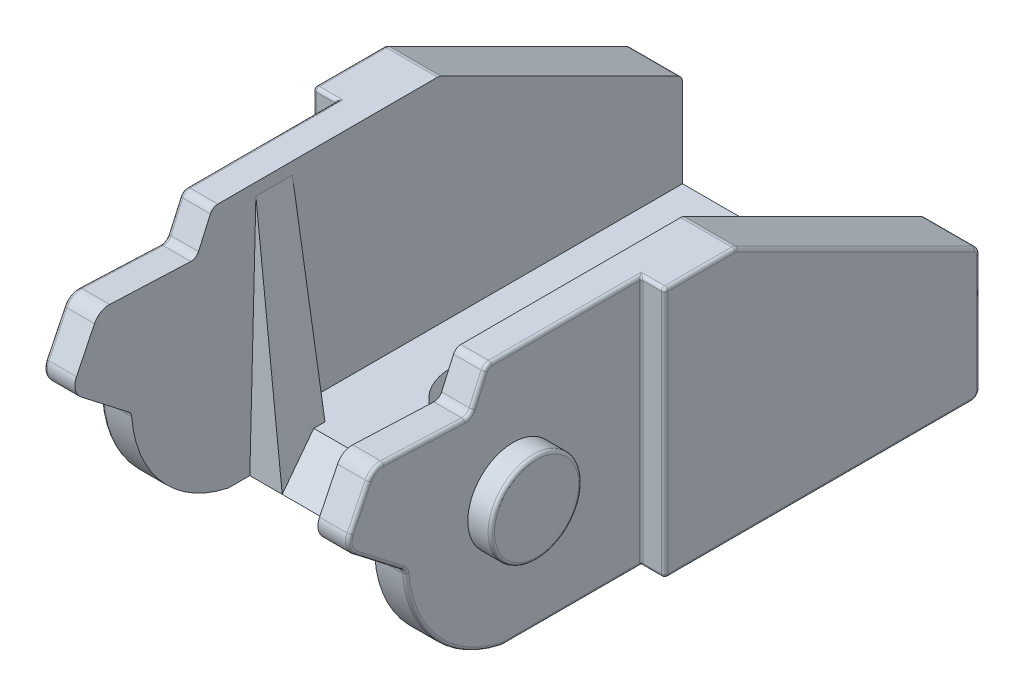
SolidWorks part; units mm, degrees
material "ABS"
ref_plane "Front Plane" through (0, 0, 0) normal (0, 0, 1) x (1, 0, 0)
ref_plane "Top Plane" through (0, 0, 0) normal (0, 1, 0) x (1, 0, 0)
ref_plane "Right Plane" through (0, 0, 0) normal (1, 0, 0) x (0, 0, -1)
sketch "Sketch1" plane through (0, 0, 0) normal (1, 0, 0) x (0, 0, -1)
  line L0 (0, 0) -> (-2.8, 0) construction
  line L1 (0, 0) -> (2.8, 0) construction
  line L2 (2.8, 0) -> (7.9, 0) construction
  line L3 (7.9, 0) -> (27.35, 0) construction
  line L4 (0, 0) -> (0, 2.8) construction
  line L5 (0, 2.8) -> (0, 7.75) construction
  line L6 (0, 0) -> (0, -2.8) construction
  line L7 (0, -2.8) -> (0, -7.75) construction
  line L8 (-10.65, 7.75) -> (27.35, 7.75)
  line L9 (-10.65, -7.75) -> (27.35, -7.75)
  line L10 (27.35, 7.75) -> (27.35, -7.75)
  line L11 (-10.65, -7.75) -> (-10.65, 7.75)
  line L12 (7.9, 7.75) -> (7.9, -7.75) construction
  circle A0 centre (0, 0) radius 2.8 construction
  dimension "D1" = 5.6
  dimension "D2" = 27.35
  dimension "D3" = 5.1
  dimension "D4" = 15.5
  dimension "D5" = 38
extrude "Boss-Extrude1" add sketch "Sketch1" along normal mid plane 21.7
sketch "Sketch2" plane through (0, 0, 0) normal (1, 0, 0) x (0, 0, -1)
  line L0 (-10.65, 7.75) -> (-10.65, -7.75)
  line L1 (-10.65, -7.75) -> (-0.65, -7.75)
  line L3 (-10.65, -7.75) -> (27.35, -7.75) construction
  line L4 (-0.65, -7.75) -> (-0.65, -0.75) construction
  line L5 (-0.65, -0.75) -> (-6.65, -0.75) construction
  line L6 (-6.65, -0.75) -> (-10.4, 2.1531)
  line L7 (-10.4, 2.1531) -> (-8.65, 5.75)
  line L8 (-8.65, 5.75) -> (-2.6552, 5.5)
  line L9 (-2.6552, 5.5) -> (-1.65, 7.75)
  line L10 (27.35, 7.75) -> (-10.65, 7.75) construction
  line L11 (-10.4, 2.1531) -> (-10.4, -0.75) construction
  line L12 (-10.4, -0.75) -> (-6.65, -0.75) construction
  line L13 (-1.65, 7.75) -> (-10.65, 7.75)
  arc A0 (-6.65, -0.75) -> (-0.65, -7.75) centre (0.8418, -0.3999) ccw
  dimension "D4" = 7.5
  dimension "D1" = 10
  dimension "D2" = 7
  dimension "D3" = 6
  dimension "D5" = 2.25
  dimension "D6" = 2
  dimension "D7" = 7
  dimension "D8" = 6
  dimension "D9" = 4
  dimension "D10" = 3.75
  dimension "D11" = 8.75
extrude "Cut-Extrude1" cut sketch "Sketch2" against normal through all both and the other way through all
fillet "Fillet1" radius 1 2 edges at (0, 5.75, 8.65) (0, 2.1531, 10.4)
fillet "Fillet2" radius 0.5 4 edges at (0, -7.75, 0.65) (0, -0.75, 6.65) (0, 5.5, 2.6552) (0, 7.75, 1.65)
sketch "Sketch4" plane through (10.85, 0, 0) normal (1, 0, 0) x (0, 0, -1)
  line L0 (7.9, 7.75) -> (7.9, -7.75) construction
  line L1 (7.9, 7.75) -> (7.9, -7.75)
  line L7 (-0.5989, -7.75) -> (27.35, -7.75)
  line L8 (27.35, -7.75) -> (27.35, 7.75)
  line L9 (27.35, 7.75) -> (-1.3258, 7.75)
  line L10 (-1.7823, 7.454) -> (-2.5168, 5.8097)
  line L11 (-2.9942, 5.5141) -> (-7.9956, 5.7227)
  line L12 (-8.9365, 5.1611) -> (-10.0445, 2.8839)
  line L13 (-9.7574, 1.6556) -> (-6.829, -0.6114)
  line L14 (-0.5989, -7.75) -> (7.9, -7.75)
  line L16 (7.9, 7.75) -> (-1.3258, 7.75)
  line L17 (-1.7823, 7.454) -> (-2.5168, 5.8097)
  line L18 (-2.9942, 5.5141) -> (-7.9956, 5.7227)
  line L19 (-8.9365, 5.1611) -> (-10.0445, 2.8839)
  line L20 (-9.7574, 1.6556) -> (-6.829, -0.6114)
  circle A0 centre (0, 0) radius 2.8 construction
  circle A1 centre (0, 0) radius 2.8
  arc A7 (-6.6366, -0.9688) -> (-0.7018, -7.7393) centre (0.8418, -0.3999) ccw
  arc A8 (-0.7018, -7.7393) -> (-0.5989, -7.75) centre (-0.5989, -7.25) ccw
  arc A9 (-1.3258, 7.75) -> (-1.7823, 7.454) centre (-1.3258, 7.25) ccw
  arc A10 (-2.9942, 5.5141) -> (-2.5168, 5.8097) centre (-2.9733, 6.0137) ccw
  arc A11 (-7.9956, 5.7227) -> (-8.9365, 5.1611) centre (-8.0373, 4.7236) ccw
  arc A12 (-10.0445, 2.8839) -> (-9.7574, 1.6556) centre (-9.1452, 2.4464) ccw
  arc A13 (-6.6366, -0.9688) -> (-6.829, -0.6114) centre (-7.1351, -1.0068) ccw
  arc A14 (-6.6366, -0.9688) -> (-0.7018, -7.7393) centre (0.8418, -0.3999) ccw
  arc A15 (-0.7018, -7.7393) -> (-0.5989, -7.75) centre (-0.5989, -7.25) ccw
  arc A16 (-1.3258, 7.75) -> (-1.7823, 7.454) centre (-1.3258, 7.25) ccw
  arc A17 (-2.9942, 5.5141) -> (-2.5168, 5.8097) centre (-2.9733, 6.0137) ccw
  arc A18 (-7.9956, 5.7227) -> (-8.9365, 5.1611) centre (-8.0373, 4.7236) ccw
  arc A19 (-10.0445, 2.8839) -> (-9.7574, 1.6556) centre (-9.1452, 2.4464) ccw
  arc A20 (-6.6366, -0.9688) -> (-6.829, -0.6114) centre (-7.1351, -1.0068) ccw
  dimension "D1" = 0
extrude "Cut-Extrude2" cut sketch "Sketch4" against normal blind 1.45
mirror "Mirror1" about plane through (0, 0, 0) normal (1, 0, 0) of "Cut-Extrude2"
sketch "Sketch5" plane through (0, 0, -27.35) normal (0, 0, -1) x (-1, 0, 0)
  line L0 (0, 0) -> (0, 7.75) construction
  line L1 (-10.85, 7.75) -> (10.85, 7.75) construction
  line L2 (0, 0) -> (0, -5.5) construction
  line L3 (-7.5, 7.75) -> (7.5, 7.75)
  line L4 (-7.5, 7.75) -> (-7.5, -5.5)
  line L5 (-7.5, -5.5) -> (7.5, -5.5)
  line L6 (7.5, 7.75) -> (7.5, -5.5)
  line L7 (0, -5.5) -> (0, -7.75) construction
  line L8 (-10.85, -7.75) -> (10.85, -7.75) construction
  dimension "D1" = 2.25
  dimension "D2" = 15
extrude "Cut-Extrude3" cut sketch "Sketch5" against normal through all
sketch "Sketch6" plane through (10.85, 0, 0) normal (1, 0, 0) x (0, 0, -1)
  line L0 (27.35, -7.75) -> (27.35, 0.25) construction
  line L1 (27.35, -7.75) -> (27.35, 7.75) construction
  line L2 (27.35, 0.25) -> (27.35, 7.75)
  line L3 (27.35, 7.75) -> (12.35, 7.75)
  line L4 (27.35, 7.75) -> (7.9, 7.75) construction
  line L5 (12.35, 7.75) -> (27.35, 0.25)
  dimension "D1" = 8
  dimension "D2" = 15
extrude "Cut-Extrude4" cut sketch "Sketch6" against normal up to surface (21.7 mm away) up to face at (-10.85, 0, -17.625)
sketch "Sketch8" plane through (0, -7.75, 0) normal (0, -1, 0) x (1, 0, 0)
  line L0 (0, -27.35) -> (0, -0.65) construction
  line L1 (-7.5, 4.6571) -> (7.5, 4.6571)
  line L2 (-7.5, 4.6571) -> (-7.5, -0.65)
  line L3 (-7.5, -0.65) -> (7.5, -0.65)
  line L4 (7.5, 4.6571) -> (7.5, -0.65)
  line L5 (10.85, -27.35) -> (-10.85, -27.35) construction
  line L6 (0, -0.65) -> (0, 0) construction
  line L7 (0, 0) -> (0, 4.6571) construction
  line L8 (7.5, 4.6571) -> (-7.5, 4.6571) construction
  line L9 (-7.5, -27.35) -> (-7.5, -12.35) construction
  dimension "D1" = 26.7
extrude "Cut-Extrude5" cut sketch "Sketch8" against normal through all
sketch "Sketch9" plane through (0, -7.75, 0) normal (0, -1, 0) x (1, 0, 0)
  line L0 (0, -21.35) -> (0, -27.35) construction
  line L2 (0, -17.35) -> (0, -21.35) construction
  line L3 (0, -12.35) -> (0, -17.35) construction
  line L4 (0, -12.35) -> (0, -8.35) construction
  line L5 (0, -8.35) -> (0, -0.65) construction
  line L6 (-7.5, -0.65) -> (7.5, -0.65) construction
  line L7 (0, -0.65) -> (0, 0) construction
  line L8 (-1.5, -19.35) -> (1.5, -19.35) construction
  line L9 (-1.5, -17.35) -> (1.5, -17.35)
  line L10 (-1.5, -21.35) -> (1.5, -21.35)
  line L11 (-1.5, -10.35) -> (1.5, -10.35) construction
  line L12 (-1.5, -8.35) -> (1.5, -8.35)
  line L13 (-1.5, -12.35) -> (1.5, -12.35)
  line L14 (1.5, -19.35) -> (3.5, -19.35) construction
  line L15 (-1.5, -19.35) -> (-3.5, -19.35) construction
  line L16 (1.5, -10.35) -> (3.5, -10.35) construction
  line L17 (-1.5, -10.35) -> (-3.5, -10.35) construction
  line L18 (10.85, -27.35) -> (-10.85, -27.35) construction
  arc A0 (-1.5, -17.35) -> (-1.5, -21.35) centre (-1.5, -19.35) ccw
  arc A1 (1.5, -21.35) -> (1.5, -17.35) centre (1.5, -19.35) ccw
  arc A2 (-1.5, -8.35) -> (-1.5, -12.35) centre (-1.5, -10.35) ccw
  arc A3 (1.5, -12.35) -> (1.5, -8.35) centre (1.5, -10.35) ccw
  point P14 (0, -19.35)
  point P21 (0, -10.35)
  dimension "D1" = 7
  dimension "D2" = 4
  dimension "D3" = 5
  dimension "D4" = 6
extrude "Cut-Extrude6" cut sketch "Sketch9" against normal up to surface (2.25 mm away) draft 30
sketch "Sketch10" plane through (7.5, 0, 0) normal (-1, 0, 0) x (0, 0, 1)
  line L0 (-0.65, -7.75) -> (-0.65, -5.5)
  line L1 (-0.65, -5.5) -> (-2.9, -5.5)
  line L2 (-0.65, -5.5) -> (-27.35, -5.5) construction
  line L3 (-2.9, -5.5) -> (-0.65, -7.75)
extrude "Cut-Extrude7" cut sketch "Sketch10" along normal up to surface (15 mm away) up to face at (-7.5, 0.779, -0.4023)
sketch "Sketch11" plane through (7.5, 0, 0) normal (-1, 0, 0) x (0, 0, 1)
  line L0 (-0.65, -7.75) -> (-3.65, -7.75)
  line L1 (-2.15, -7.75) -> (-2.15, 7) construction
  line L2 (-3.275, 7) -> (-1.025, 7)
  line L3 (-2.15, 7) -> (-2.15, 7.75) construction
  line L4 (1.3258, 7.75) -> (-12.35, 7.75) construction
  line L5 (-1.025, 7) -> (-0.65, -7.75)
  line L6 (-3.275, 7) -> (-3.65, -7.75)
  dimension "D1" = 3
  dimension "D2" = 2.25
  dimension "D3" = 0.75
extrude "Boss-Extrude2" add sketch "Sketch11" along normal blind 2 separate body
sketch "Sketch12" plane through (0, 0, 0) normal (0, 0, 1) x (1, 0, 0)
  line L0 (7.5, 7) -> (5.5, 7)
  line L1 (5.5, 7) -> (5.5, -7.75)
  line L2 (5.5, -7.75) -> (7.5, 7)
extrude "Cut-Extrude8" cut sketch "Sketch12" against normal through all
mirror "Mirror2" about plane through (0, 0, 0) normal (1, 0, 0) of bodies 111
combine bodies "Combine1" operation type add bodies to combine 109 111 112
fillet "Fillet3" radius 0.5 5 edges at (0, -7.75, -27.35) (9.175, 0.25, -27.35) (-9.175, 0.25, -27.35) (-9.175, 7.75, -12.35) (9.175, 7.75, -12.35)
fillet "Fillet4" radius 0.2 14 edges at (-10.85, -7.75, -17.375) (-10.85, -7.6036, -27.2036) (-10.85, -3.6545, -27.35) (-10.85, 0.2038, -27.2753) (-10.85, 4.0427, -19.7646) (-10.85, 7.7366, -12.3468) (10.85, -7.75, -17.375) (10.85, -7.6036, -27.2036) (10.85, -3.6545, -27.35) (10.85, 0.2038, -27.2753) (10.85, 4.0427, -19.7646) (10.85, 7.7366, -12.3468) (-10.85, 7.75, -10.066) (10.85, 7.75, -10.066)
sketch "Sketch13" plane through (0, -7.75, 0) normal (0, -1, 0) x (1, 0, 0)
  line L0 (0, -12.35) -> (0, -17.35) construction
  line L1 (-1.5, -12.35) -> (1.5, -12.35) construction
  line L2 (1.5, -17.35) -> (-1.5, -17.35) construction
  line L4 (-6, -12.85) -> (6, -12.85)
  line L5 (-6, -12.85) -> (-6, -16.85)
  line L6 (-6, -16.85) -> (6, -16.85)
  line L7 (6, -12.85) -> (6, -16.85)
  line L8 (-6, -12.85) -> (6, -16.85) construction
  line L9 (-6, -16.85) -> (6, -12.85) construction
  point P6 (0, -14.85)
  dimension "D1" = 4
  dimension "D2" = 12
extrude "Cut-Extrude9" cut sketch "Sketch13" against normal blind 0.8
sketch "Sketch14" plane through (0, -6.95, 0) normal (0, -1, 0) x (1, 0, 0)
  line L0 (-5.3737, -16.15) -> (6, -16.15) construction
  line L2 (6, -16.85) -> (6, -12.85) construction
  line L3 (-5.3737, -16.15) -> (-6, -16.15) construction
  line L4 (-6, -12.85) -> (-6, -16.85) construction
  line L5 (-6, -16.85) -> (6, -16.85) construction
  text T0 "10X15" font "Century Gothic" height 2.5
  dimension "D1" = 0.7
extrude "Boss-Extrude3" add sketch "Sketch14" along normal blind 0.15
fillet "Fillet5" radius 0.2 38 edges at (10.025, -7.75, -7.9) (10.7914, -7.6914, -7.9) (10.025, 7.75, -7.9) (10.7914, 7.6914, -7.9) (-10.025, -7.75, -7.9) (-10.7914, -7.6914, -7.9) (-10.025, 7.75, -7.9) (-10.7914, 7.6914, -7.9) (-9.4, -7.75, -3.6506) (-9.4, -7.7473, 0.6506) (-9.4, -5.3437, 4.7981) (-9.4, -0.7697, 6.6949) (-9.4, 0.5221, 8.2932) (-9.4, 2.2188, 10.119) (-9.4, 4.0225, 9.4905) (-9.4, 5.5822, 8.5499) (-9.4, 5.6184, 5.4949) (-9.4, 5.5886, 2.7101) (-9.4, 6.6319, 2.1495) (-9.4, 7.6695, 1.5978) (9.4, -7.75, -3.6506) (9.4, -7.7473, 0.6506) (9.4, -5.3437, 4.7981) (9.4, -0.7697, 6.6949) (9.4, 0.5221, 8.2932) (9.4, 2.2188, 10.119) (9.4, 4.0225, 9.4905) (9.4, 5.5822, 8.5499) (9.4, 5.6184, 5.4949) (9.4, 5.5886, 2.7101) (9.4, 6.6319, 2.1495) (9.4, 7.6695, 1.5978) (10.85, 0, -7.9) (-10.85, 0, -7.9) (-9.4, 7.75, -3.2871) (9.4, 7.75, -3.2871) (-10.85, 0, -2.8) (10.85, 0, -2.8)
fillet "Fillet6" radius 0.1 6 edges at (-9.3414, -7.6914, -7.9586) (-9.3414, 7.6914, -7.9586) (9.3414, -7.6914, -7.9586) (9.3414, 7.6914, -7.9586) (-9.4, 0, -7.9) (9.4, 0, -7.9)
